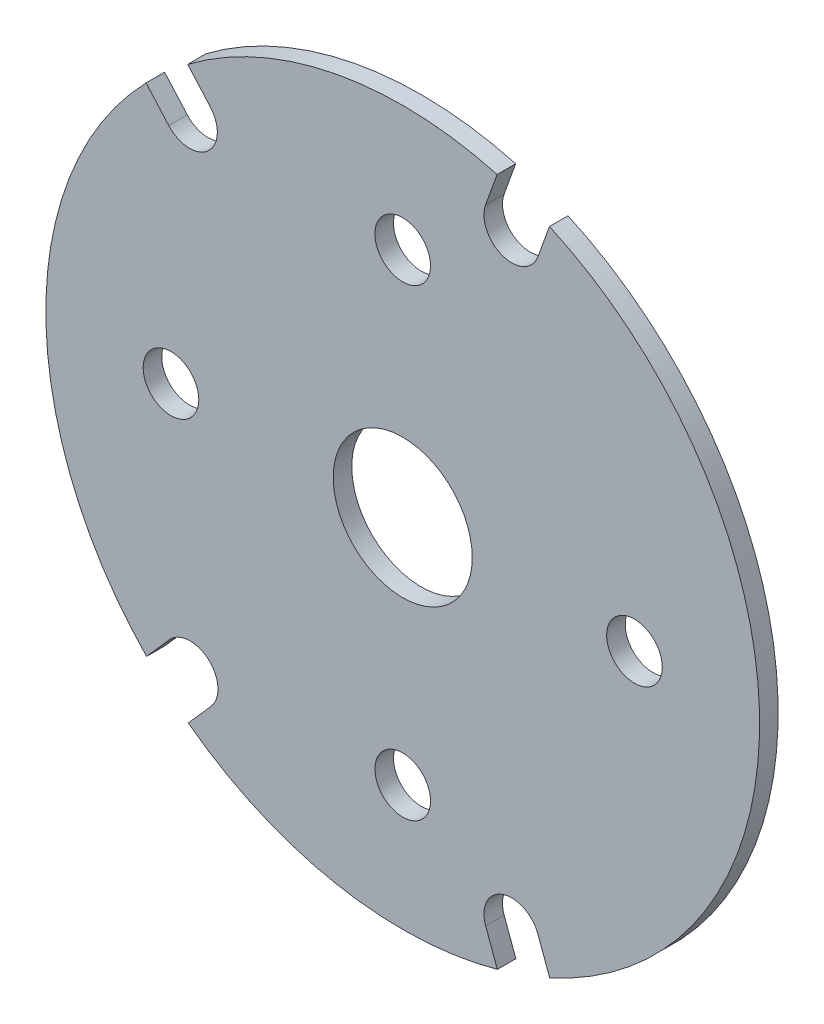
SolidWorks part; units mm, degrees
material "Acrylic (Medium-high impact)"
ref_plane "Front Plane" through (0, 0, 0) normal (0, 0, 1) x (1, 0, 0)
ref_plane "Top Plane" through (0, 0, 0) normal (0, 1, 0) x (1, 0, 0)
ref_plane "Right Plane" through (0, 0, 0) normal (1, 0, 0) x (0, 0, -1)
sketch "Model" plane through (0, 0, 0) normal (0, 0, 1) x (1, 0, 0)
  line L8 (8.9398, 33.6785) -> (10.1824, 37.1291)
  line L9 (14.5848, 31.6456) -> (15.8274, 35.0962)
  line L10 (14.5779, -31.6262) -> (15.8504, -35.0858)
  line L11 (8.9468, -33.6974) -> (10.2066, -37.1224)
  line L12 (-23.1958, 30.7279) -> (-20.7537, 27.9693)
  line L13 (-27.6884, 26.7508) -> (-25.2463, 23.9922)
  line L14 (-23.1353, -30.7735) -> (-20.6815, -27.9907)
  line L15 (-27.6357, -26.8052) -> (-25.1819, -24.0224)
  circle A0 centre (0, 0) radius 7.5
  circle A1 centre (0, 25) radius 3
  circle A2 centre (25, 0) radius 3
  circle A3 centre (0, -25) radius 3
  arc A4 (-23.1958, 30.7279) -> (10.1824, 37.1291) centre (0, 0) cw
  arc A5 (-23.1353, -30.7735) -> (10.2066, -37.1224) centre (0, 0) ccw
  circle A9 centre (-25, 0) radius 3
  arc A19 (-25.2463, 23.9922) -> (-20.7537, 27.9693) centre (-23, 25.9808) ccw
  arc A20 (-20.6815, -27.9907) -> (-25.1819, -24.0224) centre (-22.9317, -26.0066) ccw
  arc A21 (-27.6884, 26.7508) -> (-27.6357, -26.8052) centre (0, 0) ccw
  arc A31 (15.8504, -35.0858) -> (15.8274, 35.0962) centre (0, 0) ccw
  arc A32 (8.9398, 33.6785) -> (14.5848, 31.6456) centre (11.7623, 32.6621) ccw
  arc A34 (14.5779, -31.6262) -> (8.9468, -33.6974) centre (11.7623, -32.6618) ccw
  dimension "D1" = 15
  dimension "D2" = 6
  dimension "D3" = 38.5
  dimension "D4" = 3
  dimension "D5" = 8.9398
  dimension "D6" = 8.9468
  dimension "D7" = 10.1824
  dimension "D8" = 10.2066
  dimension "D9" = 11.7623
  dimension "D10" = 14.5779
  dimension "D11" = 25
  dimension "D12" = 20.6815
  dimension "D13" = 20.7537
  dimension "D14" = 22.9317
  dimension "D15" = 23
  dimension "D16" = 23.1353
  dimension "D17" = 23.1958
  dimension "D18" = 25
  dimension "D19" = 25
  dimension "D20" = 25
extrude "Boss-Extrude1" add sketch "Model" along normal blind 2
